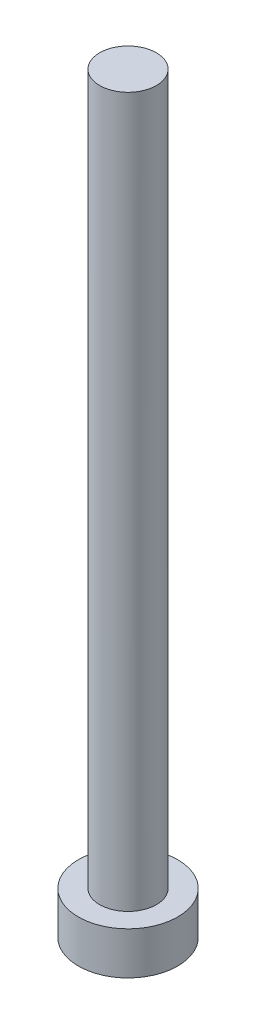
SolidWorks part; units mm, degrees
ref_plane "Front Plane" through (0, 0, 0) normal (0, 0, 1) x (1, 0, 0)
ref_plane "Top Plane" through (0, 0, 0) normal (0, 1, 0) x (1, 0, 0)
ref_plane "Right Plane" through (0, 0, 0) normal (1, 0, 0) x (0, 0, -1)
sketch "Sketch1" plane through (0, 0, 0) normal (0, 1, 0) x (1, 0, 0)
  circle A0 centre (0, 0) radius 2
  dimension "D1" = 4
extrude "Boss-Extrude1" add sketch "Sketch1" along normal blind 50
sketch "Sketch2" plane through (0, 0, 0) normal (0, -1, 0) x (1, 0, 0)
  circle A0 centre (0, 0) radius 3.5
  dimension "D1" = 7
extrude "Boss-Extrude2" add sketch "Sketch2" along normal blind 3
